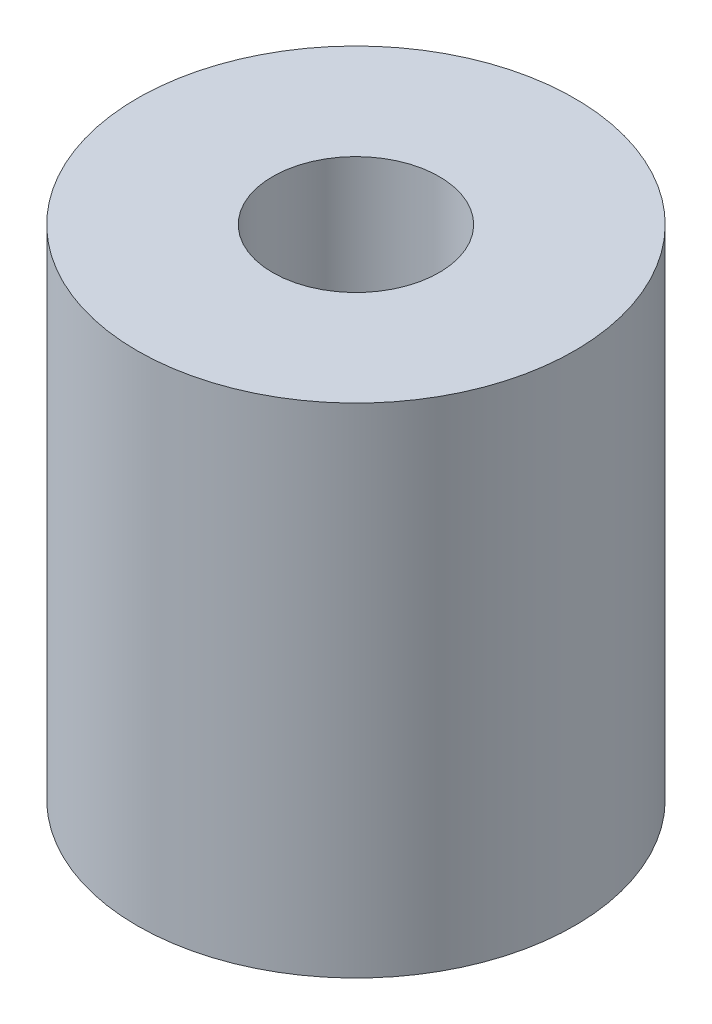
SolidWorks part; units mm, degrees
ref_plane "Front Plane" through (0, 0, 0) normal (0, 0, 1) x (1, 0, 0)
ref_plane "Top Plane" through (0, 0, 0) normal (0, 1, 0) x (1, 0, 0)
ref_plane "Right Plane" through (0, 0, 0) normal (1, 0, 0) x (0, 0, -1)
sketch "Sketch1" plane through (0, 0, 0) normal (0, 1, 0) x (1, 0, 0)
  circle A0 centre (0, 0) radius 13
  circle A1 centre (0, 0) radius 4.95
  dimension "D1" = 26
  dimension "D2" = 9.9
extrude "Boss-Extrude1" add sketch "Sketch1" along normal blind 29.6
ref_plane "Plane1" through (0, 18.6506, 0) normal (0, 1, 0) x (1, 0, 0)
sketch "Sketch2" plane through (0, 18.6506, 0) normal (0, 1, 0) x (1, 0, 0)
  circle A0 centre (0, 0) radius 4.95
extrude "Boss-Extrude3" add sketch "Sketch2" against normal offset from surface (8.6506 mm away) 10 up to face at (0, 0, 13)
sketch "Sketch3" plane through (0, 0, 0) normal (0, -1, 0) x (1, 0, 0)
  circle A1 centre (0, 0) radius 13
  circle A2 centre (0, 0) radius 13
  circle A3 centre (0, 0) radius 3.9
  circle A4 centre (0, 0) radius 4.95 construction
  circle A5 centre (0, 0) radius 4.95
  circle M5 centre (0, 0) radius 4.95
  dimension "D2" = 7.8
  dimension "D1" = 0
extrude "Boss-Extrude4" add sketch "Sketch3" against normal blind 11.85 contours A3 M5
